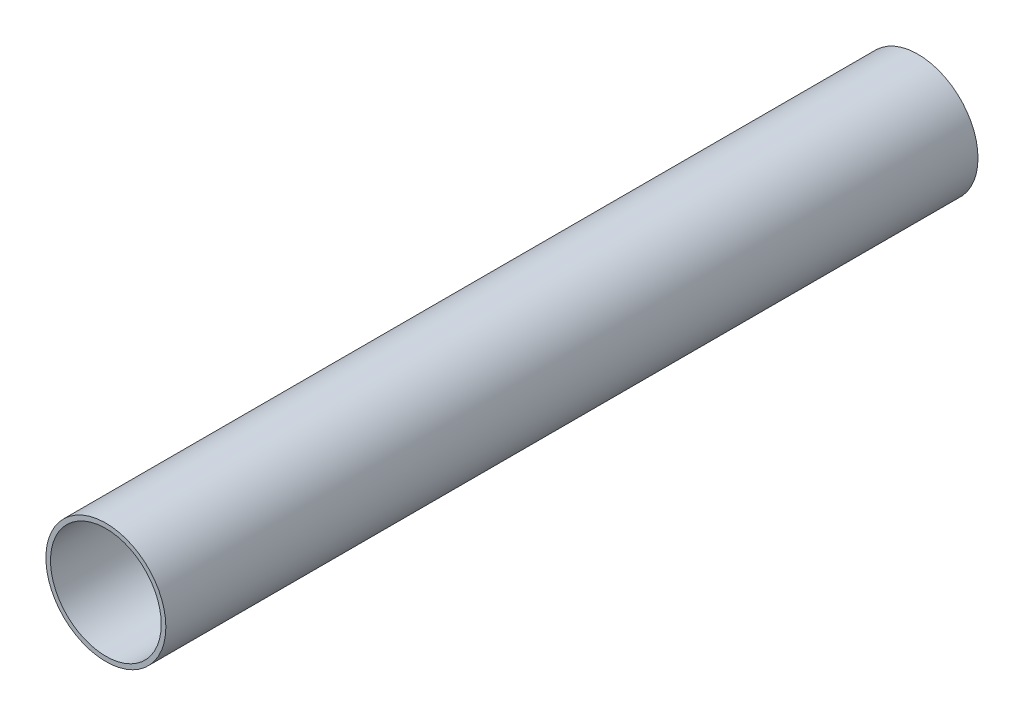
SolidWorks part; units mm, degrees
ref_plane "Front Plane" through (0, 0, 0) normal (0, 0, 1) x (1, 0, 0)
ref_plane "Top Plane" through (0, 0, 0) normal (0, 1, 0) x (1, 0, 0)
ref_plane "Right Plane" through (0, 0, 0) normal (1, 0, 0) x (0, 0, -1)
sketch "Sketch1" plane through (0, 0, 0) normal (0, 0, 1) x (1, 0, 0)
  circle A0 centre (0, 0) radius 20.6375
  circle A1 centre (0, 0) radius 19.05
  dimension "D1" = 41.275
  dimension "D2" = 1.5875
extrude "Boss-Extrude1" add sketch "Sketch1" along normal blind 279.4
